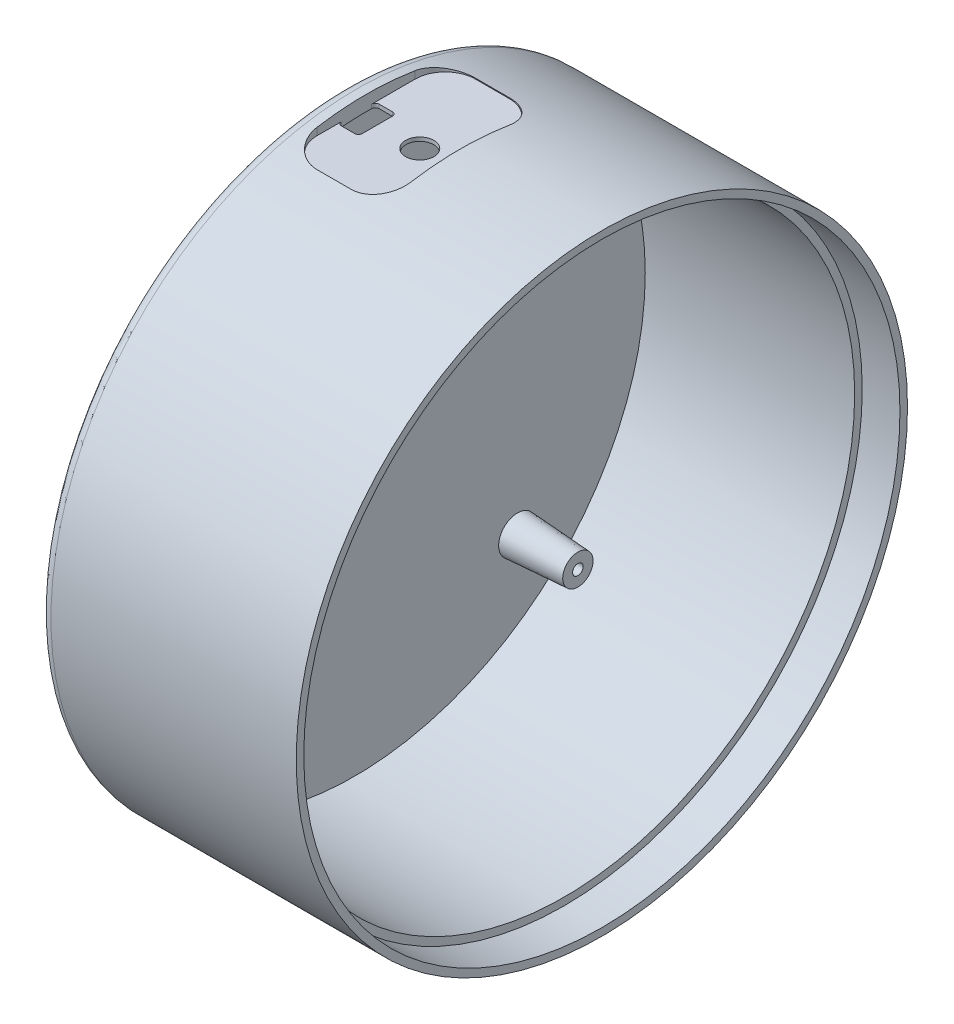
SolidWorks part; units mm, degrees
ref_plane "Front Plane" through (0, 0, 0) normal (0, 0, 1) x (1, 0, 0)
ref_plane "Top Plane" through (0, 0, 0) normal (0, 1, 0) x (1, 0, 0)
ref_plane "Right Plane" through (0, 0, 0) normal (1, 0, 0) x (0, 0, -1)
sketch "Sketch1" plane through (0, 0, 0) normal (1, 0, 0) x (0, 0, -1)
  circle A0 centre (0, 0) radius 81
  dimension "D1" = 162
extrude "Boss-Extrude1" add sketch "Sketch1" along normal blind 2.5
sketch "Sketch2" plane through (2.5, 0, 0) normal (1, 0, 0) x (0, 0, -1)
  circle A0 centre (0, 0) radius 77
  circle A1 centre (0, 0) radius 81
  dimension "D1" = 154
  dimension "D2" = 162
extrude "Boss-Extrude2" add sketch "Sketch2" along normal blind 65.5
sketch "Sketch4" plane through (2.5, 0, 0) normal (1, 0, 0) x (0, 0, -1)
  line L0 (0, 78.6345) -> (0, -85.661) construction
  line L1 (-89.8975, 0) -> (85.1443, 0) construction
  circle A0 centre (43.14, 43.135) radius 5
  circle A1 centre (-43.14, 43.135) radius 5
  circle A2 centre (43.14, -43.135) radius 5
  circle A3 centre (-43.14, -43.135) radius 5
  dimension "D1" = 10
  dimension "D2" = 43.135
  dimension "D3" = 43.14
extrude "Boss-Extrude3" add sketch "Sketch4" along normal blind 16 draft 3.5
sketch "Sketch6" plane through (18.5, 0, 0) normal (1, 0, 0) x (0, 0, -1)
  line L0 (0, 86.8722) -> (0, -106.1072) construction
  line L1 (-114.3875, 0) -> (111.4469, 0) construction
  circle A0 centre (-43.14, 43.135) radius 1.4
  circle A1 centre (43.14, 43.135) radius 1.4
  circle A2 centre (-43.14, -43.135) radius 1.4
  circle A3 centre (43.14, -43.135) radius 1.4
  dimension "D1" = 2.8
extrude "Cut-Extrude2" cut sketch "Sketch6" against normal blind 7
sketch "Sketch7" plane through (68, 0, 0) normal (1, 0, 0) x (0, 0, -1)
  circle A0 centre (0, 0) radius 79
  dimension "D1" = 158
extrude "Cut-Extrude3" cut sketch "Sketch7" against normal blind 10
fillet "Fillet1" radius 3 1 edges at (0, 0, -81)
sketch "Sketch8" plane through (2.5, 0, 0) normal (1, 0, 0) x (0, 0, -1)
  line L0 (0, 86.7515) -> (0, -96.2523) construction
  line L1 (-99.08, 0) -> (117.6292, 0) construction
  line L2 (0, 0) -> (24.9281, 95.8356) construction
  line L3 (19.3837, 74.5203) -> (17.1828, 75.0928) construction
  line L4 (-27.5716, 41.0459) -> (25.894, 41.0459) construction
  line L5 (18.48, 71.0459) -> (-18.48, 71.0459) construction
  line L6 (0, 77) -> (-4.8238, 77) construction
  line L7 (18.48, 74.0459) -> (-18.48, 74.0459) construction
  circle A0 centre (18.48, 71.0459) radius 3
  circle A1 centre (0, 0) radius 77 construction
  circle A2 centre (-18.48, 71.0459) radius 3
  circle A3 centre (18.48, 11.0459) radius 3
  circle A4 centre (-18.48, 11.0459) radius 3
  dimension "D1" = 18.48
  dimension "D2" = 6
  dimension "D4" = 30
  dimension "D3" = 3.59
extrude "Boss-Extrude4" add sketch "Sketch8" along normal blind 4 draft 5
sketch "Sketch9" plane through (6.5, 0, 0) normal (1, 0, 0) x (0, 0, -1)
  circle A0 centre (18.48, 71.0459) radius 1
  circle A1 centre (-18.48, 71.0459) radius 1
  circle A2 centre (-18.48, 11.0459) radius 1
  circle A3 centre (18.48, 11.0459) radius 1
  dimension "D1" = 2
  dimension "D2" = 2
extrude "Cut-Extrude4" cut sketch "Sketch9" against normal blind 3
ref_plane "Plane1" through (0, 81, 0) normal (0, 1, 0) x (1, 0, 0)
sketch "Sketch10" plane through (0, 81, 0) normal (0, 1, 0) x (1, 0, 0)
  line L0 (-31.2754, 0) -> (107.1078, 0) construction
  line L1 (18, 168.7004) -> (18, -170.9241) construction
  line L2 (0, 78) -> (0, -78) construction
  line L4 (13.5, 21) -> (22.5, 21)
  line L5 (5.5, 13) -> (5.5, -13)
  line L6 (13.5, -21) -> (22.5, -21)
  line L7 (30.5, 13) -> (30.5, -13)
  line L8 (5.5, 21) -> (30.5, -21) construction
  line L9 (5.5, -21) -> (30.5, 21) construction
  arc A0 (22.5, -21) -> (30.5, -13) centre (22.5, -13) ccw
  arc A1 (5.5, -13) -> (13.5, -21) centre (13.5, -13) ccw
  arc A2 (13.5, 21) -> (5.5, 13) centre (13.5, 13) ccw
  arc A3 (22.5, 21) -> (30.5, 13) centre (22.5, 13) cw
  point P7 (18, 0)
  point P12 (0, 0)
  dimension "D4" = 8
  dimension "D1" = 18
  dimension "D2" = 25
  dimension "D3" = 21
extrude "Cut-Extrude5" cut sketch "Sketch10" against normal blind 3
sketch "Sketch14" plane through (0, 78, 0) normal (0, 1, 0) x (1, 0, 0)
  line L0 (-18.0283, 0) -> (85.8021, 0) construction
  line L1 (8.8, 106.8846) -> (8.8, -125.7003) construction
  line L2 (0, 78) -> (0, -78) construction
  line L3 (6.5, 2.5) -> (10, 2.5)
  line L4 (5.5, 13) -> (5.5, -13) construction
  line L5 (11, 1.5) -> (11, -6.5)
  line L6 (10, -7.5) -> (6.5, -7.5)
  line L7 (5.5, -6.5) -> (5.5, 1.5)
  arc A0 (11, -6.5) -> (10, -7.5) centre (10, -6.5) cw
  arc A1 (6.5, -7.5) -> (5.5, -6.5) centre (6.5, -6.5) cw
  arc A2 (6.5, 2.5) -> (5.5, 1.5) centre (6.5, 1.5) ccw
  arc A3 (10, 2.5) -> (11, 1.5) centre (10, 1.5) cw
  point P15 (11, -7.5)
  point P18 (5.5, -7.5)
  point P21 (5.5, 2.5)
  dimension "D5" = 1
  dimension "D1" = 8.8
  dimension "D2" = 2.5
  dimension "D3" = 7.5
  dimension "D4" = 5.5
extrude "Cut-Extrude7" cut sketch "Sketch14" against normal blind 3 contours L7 A2 L3 A3 L5 A0 L6 A1
sketch "Sketch15" plane through (0, 78, 0) normal (0, 1, 0) x (1, 0, 0)
  line L0 (-19.838, 0) -> (77.8847, 0) construction
  line L6 (6.5, 2.5) -> (10, 2.5) construction
  line L8 (30.5, 13) -> (30.5, -13) construction
  circle A0 centre (22.047, -2.3059) radius 3.75
  dimension "D1" = 7.5
  dimension "D2" = 4.8059
  dimension "D3" = 8.453
extrude "Cut-Extrude8" cut sketch "Sketch15" against normal blind 3
